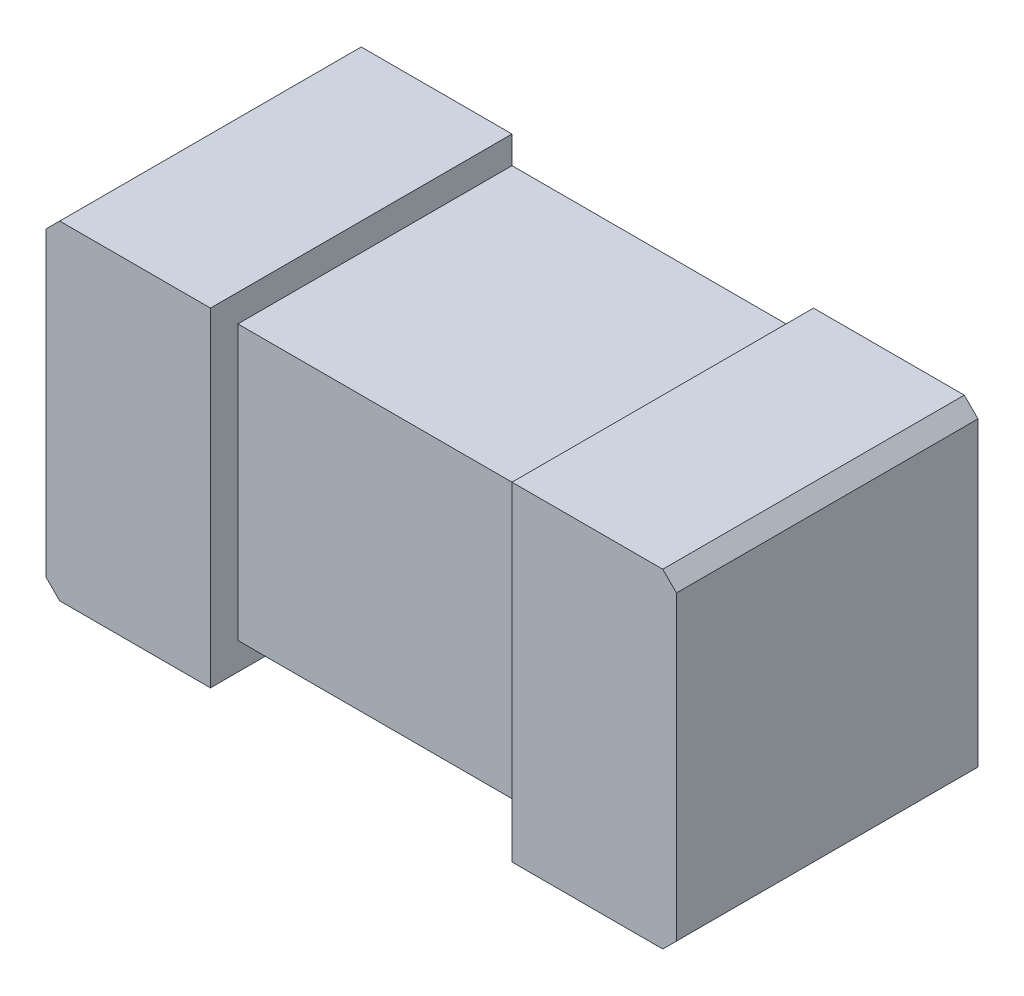
SolidWorks part; units mm, degrees
ref_plane "Front" through (0, 0, 0) normal (0, 0, 1) x (1, 0, 0)
ref_plane "Top" through (0, 0, 0) normal (0, 1, 0) x (1, 0, 0)
ref_plane "Right" through (0, 0, 0) normal (1, 0, 0) x (0, 0, -1)
sketch "COMPONENT_OUTLINE" plane through (0, 0, 0) normal (0, 0, 1) x (1, 0, 0)
  line L0 (0.55, 0.3) -> (-0.55, 0.3)
  line L1 (-0.55, 0.3) -> (-0.575, 0.275)
  line L2 (-0.575, 0.275) -> (-0.575, -0.275)
  line L3 (-0.575, -0.275) -> (-0.55, -0.3)
  line L4 (-0.55, -0.3) -> (0.55, -0.3)
  line L5 (0.55, -0.3) -> (0.575, -0.275)
  line L6 (0.575, -0.275) -> (0.575, 0.275)
  line L7 (0.575, 0.275) -> (0.55, 0.3)
extrude "Extrude1" add sketch "COMPONENT_OUTLINE" along normal blind 0.55
sketch "Sketch1" plane through (0, 0, 0.55) normal (0, 0, 1) x (1, 0, 0)
  line L0 (-0.275, -0.3) -> (-0.275, -0.25)
  line L1 (0.275, 0.25) -> (0.275, 0.3)
  line L2 (0.275, -0.3) -> (0.275, -0.25)
  line L11 (-0.275, 0.275) -> (-0.275, -0.275)
  line L12 (-0.275, 0.3) -> (-0.275, 0.25)
  line L16 (0.525, 0.25) -> (-0.525, 0.25)
  line L17 (-0.525, 0.25) -> (-0.525, -0.25)
  line L18 (-0.525, -0.25) -> (0.525, -0.25)
  line L19 (0.525, -0.25) -> (0.525, 0.25)
  line L20 (0.275, 0.25) -> (-0.275, 0.25)
  line L22 (-0.275, -0.25) -> (0.275, -0.25)
  line L31 (0.575, 0.275) -> (0.55, 0.3)
  line L32 (0.55, 0.3) -> (-0.55, 0.3)
  line L33 (-0.55, 0.3) -> (-0.575, 0.275)
  line L34 (-0.575, 0.275) -> (-0.575, -0.275)
  line L35 (-0.575, -0.275) -> (-0.55, -0.3)
  line L36 (-0.55, -0.3) -> (0.55, -0.3)
  line L37 (0.55, -0.3) -> (0.575, -0.275)
  line L38 (0.575, -0.275) -> (0.575, 0.275)
  line L40 (0.275, 0.3) -> (-0.275, 0.3)
  line L44 (-0.275, -0.3) -> (0.275, -0.3)
  dimension "D1" = 0.05
  dimension "D2" = 0.3
  dimension "D4" = 0
extrude "Cut-Extrude1" cut sketch "Sketch1" against normal blind 10
sketch "Sketch2" plane through (0, -0.25, 0) normal (0, -1, 0) x (1, 0, 0)
  line L0 (0.275, 0.5) -> (-0.275, 0.5)
  line L4 (0.275, 0) -> (0.275, 0.55)
  line L5 (0.275, 0.55) -> (-0.275, 0.55)
  line L6 (-0.275, 0.55) -> (-0.275, 0)
  line L7 (-0.275, 0) -> (0.275, 0)
  line L8 (0.275, 0.5) -> (0.275, 0.55)
  line L9 (0.275, 0.55) -> (-0.275, 0.55)
  line L10 (-0.275, 0.55) -> (-0.275, 0.5)
  dimension "D2" = 0.05
  dimension "D1" = 0
extrude "Cut-Extrude2" cut sketch "Sketch2" against normal blind 10
